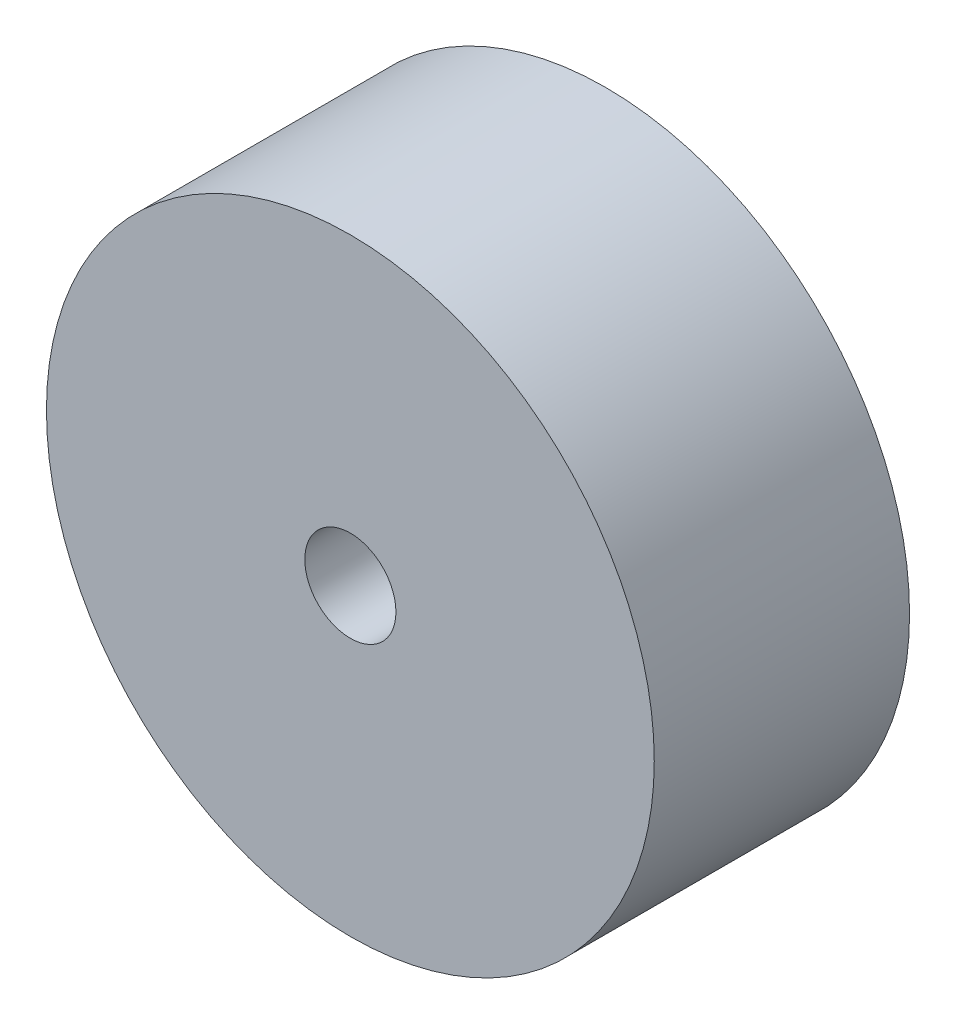
SolidWorks part; units mm, degrees
material "Borracha"
ref_plane "Plano frontal" through (0, 0, 0) normal (0, 0, 1) x (1, 0, 0)
ref_plane "Plano superior" through (0, 0, 0) normal (0, 1, 0) x (1, 0, 0)
ref_plane "Plano direito" through (0, 0, 0) normal (1, 0, 0) x (0, 0, -1)
sketch "Esboço1" plane through (0, 0, 0) normal (0, 0, 1) x (1, 0, 0)
  circle A0 centre (0, 0) radius 50
  dimension "D1" = 100
extrude "Ressalto-extrusão1" add sketch "Esboço1" along normal blind 42
sketch "Esboço2" plane through (0, 0, 42) normal (0, 0, 1) x (1, 0, 0)
  circle A0 centre (0, 0) radius 7.5
  dimension "D1" = 15
extrude "Corte-extrusão1" cut sketch "Esboço2" against normal through all
